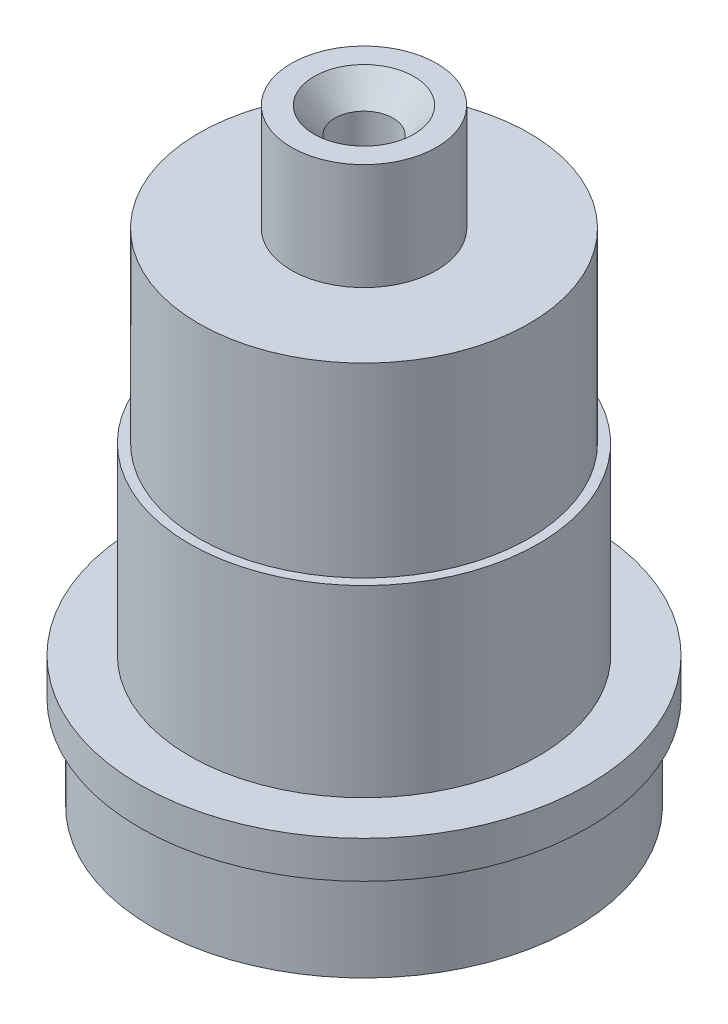
SolidWorks part; units mm, degrees
material "6061-T6 (SS)"
ref_plane "Front Plane" through (0, 0, 0) normal (0, 0, 1) x (1, 0, 0)
ref_plane "Top Plane" through (0, 0, 0) normal (0, 1, 0) x (1, 0, 0)
ref_plane "Right Plane" through (0, 0, 0) normal (1, 0, 0) x (0, 0, -1)
sketch "Sketch1" plane through (0, 0, 0) normal (0, 1, 0) x (1, 0, 0)
  circle A0 centre (0, 0) radius 23.0505
  dimension "D1" = 46.101
extrude "Boss-Extrude1" add sketch "Sketch1" along normal blind 10.16
sketch "Sketch2" plane through (0, 10.16, 0) normal (0, 1, 0) x (1, 0, 0)
  circle A0 centre (0, 0) radius 24.4856
  dimension "D1" = 48.9712
extrude "Boss-Extrude2" add sketch "Sketch2" along normal blind 4.064
sketch "Sketch3" plane through (0, 14.224, 0) normal (0, 1, 0) x (1, 0, 0)
  circle A0 centre (0, 0) radius 19.05
  dimension "D1" = 38.1
extrude "Boss-Extrude3" add sketch "Sketch3" along normal blind 20.066
sketch "Sketch4" plane through (0, 34.29, 0) normal (0, 1, 0) x (1, 0, 0)
  circle A0 centre (0, 0) radius 18.034
  dimension "D1" = 36.068
extrude "Boss-Extrude4" add sketch "Sketch4" along normal blind 20.32
sketch "Sketch5" plane through (0, 54.61, 0) normal (0, 1, 0) x (1, 0, 0)
  circle A0 centre (0, 0) radius 7.9375
  dimension "D1" = 15.875
extrude "Boss-Extrude5" add sketch "Sketch5" along normal blind 11.6332
sketch "Sketch6" plane through (0, 0, 0) normal (0, 0, 1) x (1, 0, 0)
  line L0 (6.35, 66.2432) -> (6.35, 67.7672)
  line L1 (7.9375, 66.2432) -> (-7.9375, 66.2432) construction
  line L2 (6.35, 67.7672) -> (3.3655, 67.7672)
  line L3 (3.3655, 67.7672) -> (3.3655, 71.8312)
  line L4 (3.3655, 71.8312) -> (7.112, 71.8312)
  line L5 (7.112, 71.8312) -> (7.112, 76.1492)
  line L6 (7.112, 76.1492) -> (0, 76.1492)
  line L7 (0, 76.1492) -> (0, 66.2432)
  line L8 (0, 66.2432) -> (6.35, 66.2432)
  dimension "D1" = 6.35
  dimension "D2" = 1.524
  dimension "D3" = 4.064
  dimension "D4" = 4.318
  dimension "D5" = 7.112
  dimension "D6" = 3.3655
revolve "Revolve1" [suppressed] add sketch "Sketch6" angle 360 about L7
fillet "Fillet1" [suppressed] radius 1.27
sketch "Sketch7" plane through (0, 66.2432, 0) normal (0, 1, 0) x (1, 0, 0)
  circle A0 centre (0, 0) radius 3.175
  dimension "D1" = 6.35
extrude "Cut-Extrude1" cut sketch "Sketch7" against normal blind 17.018
chamfer "Chamfer1" distance 2.286 distance2 2.794 1 edges at (0, 66.2432, 3.175)
